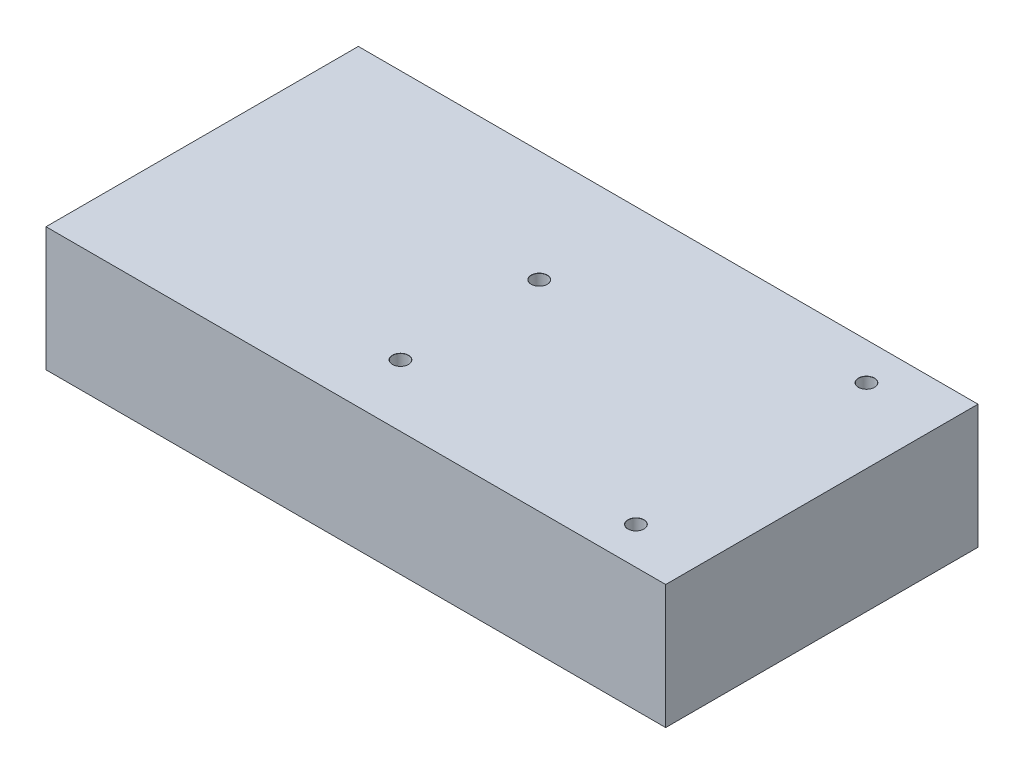
SolidWorks part; units mm, degrees
ref_plane "前视基准面" through (0, 0, 0) normal (0, 0, 1) x (1, 0, 0)
ref_plane "上视基准面" through (0, 0, 0) normal (0, 1, 0) x (1, 0, 0)
ref_plane "右视基准面" through (0, 0, 0) normal (1, 0, 0) x (0, 0, -1)
sketch "Sketch1" plane through (0, 0, 0) normal (0, 1, 0) x (1, 0, 0)
  line L1 (-62.5, -31.5) -> (62.5, -31.5)
  line L2 (-62.5, -31.5) -> (-62.5, 31.5)
  line L3 (-62.5, 31.5) -> (62.5, 31.5)
  line L4 (62.5, -31.5) -> (62.5, 31.5)
  line L5 (-62.5, -31.5) -> (62.5, 31.5) construction
  line L6 (-62.5, 31.5) -> (62.5, -31.5) construction
  point P0 (0, 0)
  dimension "D1" = 63
  dimension "D2" = 125
extrude "Boss-Extrude1" add sketch "Sketch1" along normal blind 25 contours L2 L1 L4 L3
hole_wizard "M3 Clearance Hole1" positions "Sketch5" profile "Sketch4" hole size "M3" standard "GB" end condition through all
sketch "Sketch5" plane through (0, 25, 0) normal (0, 1, 0) x (1, 0, 0)
  line L0 (62.5, -31.5) -> (62.5, 31.5) construction
  line L1 (-62.5, -31.5) -> (62.5, -31.5) construction
  line L2 (-62.5, 31.5) -> (62.5, 31.5) construction
  point P0 (47.5, 24)
  point P2 (49, -24)
  point P4 (-3.5, 9)
  point P6 (-3.5, -19)
  point P19 (38.4162, 19.7898)
  dimension "D1" = 13.5
  dimension "D2" = 7.5
  dimension "D3" = 7.5
  dimension "D4" = 15
  dimension "D5" = 22.5
  dimension "D6" = 66
  dimension "D7" = 12.5
  dimension "D8" = 66
sketch "Sketch4" plane through (47.5, 25, -24) normal (1, 0, 0) x (0, 0, 1)
  line L0 (0, 0) -> (0, 25)
  line L1 (0, 25) -> (1.6, 25)
  line L2 (1.6, 25) -> (1.6, 0.025)
  line L3 (1.6, 0.025) -> (1.625, 0)
  line L5 (1.625, 0) -> (0, 0)
  line L6 (-1.6, 0.025) -> (-1.625, 0) construction
  line L11 (0, -6.35) -> (0, 107.95) construction
  dimension "Thru Hole Dia." = 3.2
  dimension "Thru Hole Depth" = 25
  dimension "Near C'Sink Dia." = 3.25
  dimension "Near C'Sink Angle" = 90
